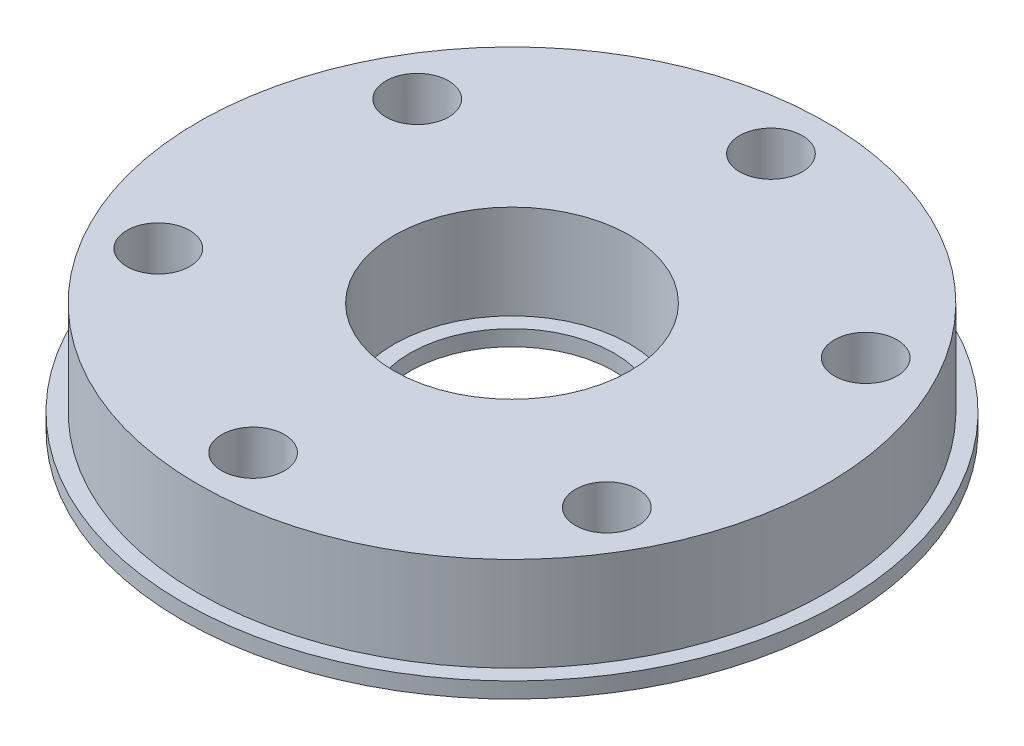
SolidWorks part; units mm, degrees
ref_plane "Front Plane" through (0, 0, 0) normal (0, 0, 1) x (1, 0, 0)
ref_plane "Top Plane" through (0, 0, 0) normal (0, 1, 0) x (1, 0, 0)
ref_plane "Right Plane" through (0, 0, 0) normal (1, 0, 0) x (0, 0, -1)
sketch "Sketch1" plane through (0, 0, 0) normal (0, 1, 0) x (1, 0, 0)
  circle A0 centre (0, 0) radius 20
  circle A1 centre (0, 0) radius 7.5
  dimension "D1" = 40
  dimension "D2" = 15
extrude "Boss-Extrude1" add sketch "Sketch1" along normal blind 6
sketch "Sketch2" plane through (0, 6, 0) normal (0, 1, 0) x (1, 0, 0)
  circle A0 centre (0, 16.5) radius 2
  dimension "D1" = 16.5
  dimension "D2" = 4
extrude "Cut-Extrude1" cut sketch "Sketch2" against normal through all
pattern_circular "CirPattern2" count 6 over 360 about axis through (0, 0, 0) along (0, 1, 0) of "Cut-Extrude1"
sketch "Sketch3" plane through (0, 0, 0) normal (0, 1, 0) x (1, 0, 0)
  circle A0 centre (-14.2894, -8.25) radius 2 construction
  circle A1 centre (0, -16.5) radius 2 construction
  circle A2 centre (14.2894, -8.25) radius 2 construction
  circle A3 centre (14.2894, 8.25) radius 2 construction
  circle A4 centre (0, 0) radius 21
  circle A5 centre (0, 16.5) radius 2 construction
  circle A6 centre (-14.2894, 8.25) radius 2 construction
  circle A7 centre (0, 0) radius 6.5
  circle A8 centre (-14.2894, -8.25) radius 2
  circle A9 centre (0, -16.5) radius 2
  circle A10 centre (14.2894, -8.25) radius 2
  circle A11 centre (14.2894, 8.25) radius 2
  circle A13 centre (0, 16.5) radius 2
  circle A14 centre (-14.2894, 8.25) radius 2
  circle A19 centre (0, 0) radius 20 construction
  circle A20 centre (0, 0) radius 7.5 construction
  dimension "D1" = 1
  dimension "D2" = 1
extrude "Boss-Extrude2" add sketch "Sketch3" against normal blind 1
